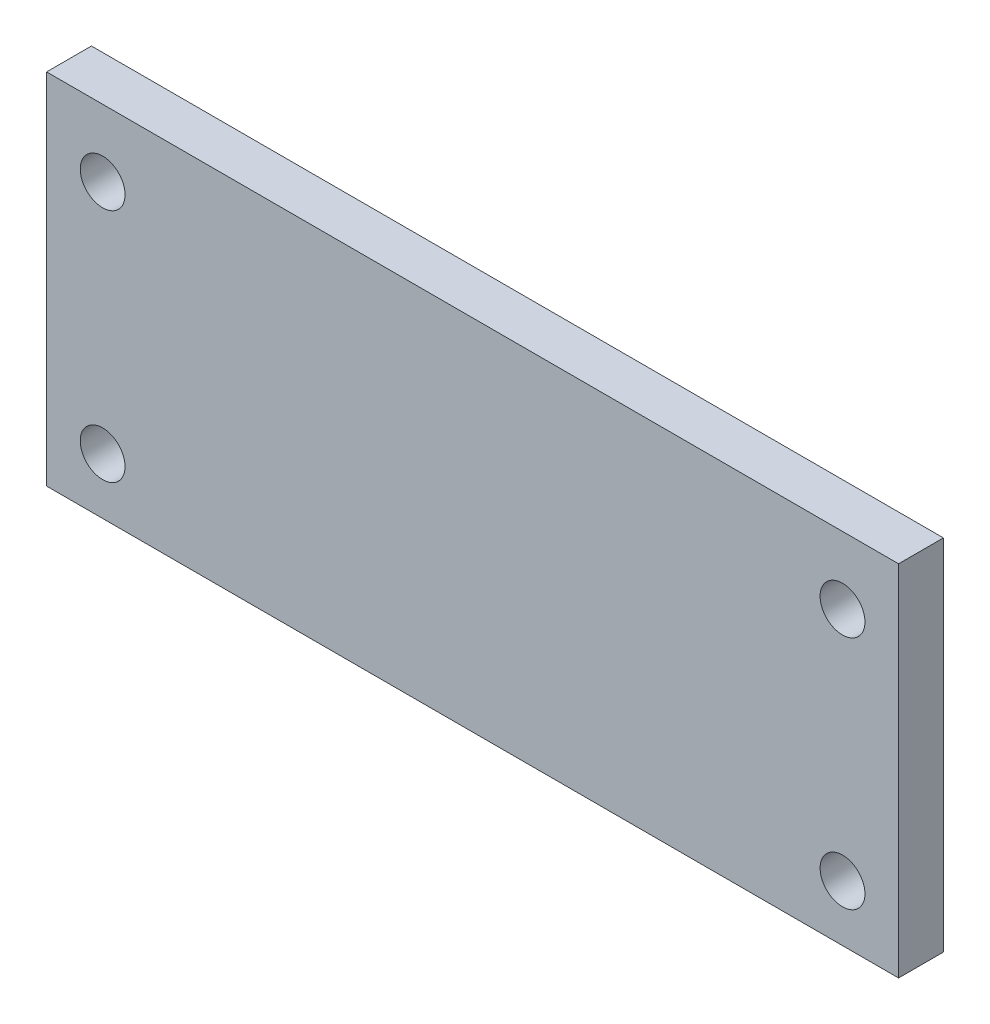
SolidWorks part; units mm, degrees
ref_plane "Спереди" through (0, 0, 0) normal (0, 0, 1) x (1, 0, 0)
ref_plane "Сверху" through (0, 0, 0) normal (0, 1, 0) x (1, 0, 0)
ref_plane "Справа" through (0, 0, 0) normal (1, 0, 0) x (0, 0, -1)
sketch "Эскиз1" plane through (0, 0, 0) normal (0, 0, 1) x (1, 0, 0)
  line L0 (5, 32) -> (5, 0) construction
  line L1 (0, 0) -> (76, 0)
  line L2 (0, 0) -> (0, 32)
  line L3 (0, 32) -> (76, 32)
  line L4 (76, 0) -> (76, 32)
  line L5 (71, 32) -> (71, 0) construction
  line L7 (5, 5) -> (71, 5) construction
  line L9 (5, 26) -> (71, 26) construction
  circle A0 centre (5, 5) radius 2
  circle A1 centre (5, 26) radius 2
  circle A2 centre (71, 26) radius 2
  circle A3 centre (71, 5) radius 2
  point P9 (71, 16)
  dimension "D7" = 4
  dimension "D1" = 66
  dimension "D2" = 32
  dimension "D3" = 5
  dimension "D4" = 5
  dimension "D5" = 5
  dimension "D6" = 6
extrude "Бобышка-Вытянуть1" add sketch "Эскиз1" along normal blind 4
